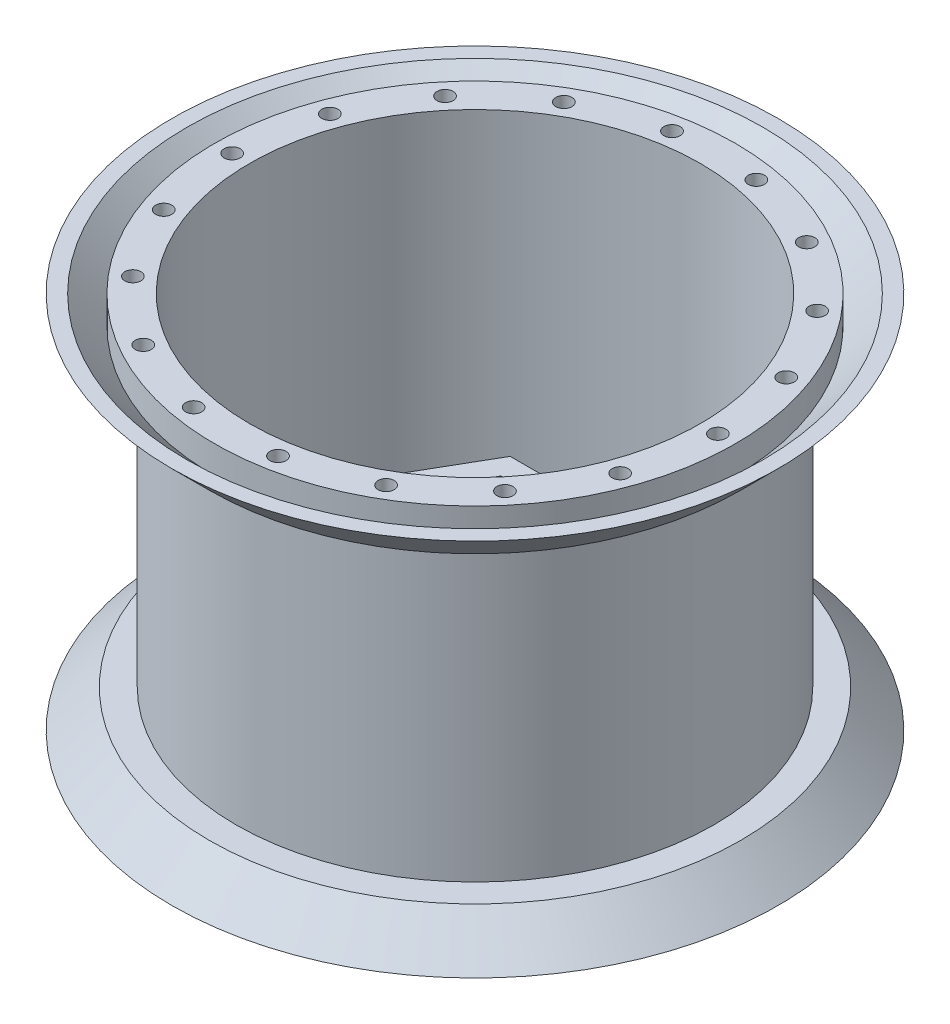
SolidWorks part; units mm, degrees
material "ABS"
ref_plane "Front Plane" through (0, 0, 0) normal (0, 0, 1) x (1, 0, 0)
ref_plane "Top Plane" through (0, 0, 0) normal (0, 1, 0) x (1, 0, 0)
ref_plane "Right Plane" through (0, 0, 0) normal (1, 0, 0) x (0, 0, -1)
sketch "Sketch1" plane through (0, 0, 0) normal (1, 0, 0) x (0, 0, -1)
  line L0 (0, 0) -> (0, 63.5) construction
  line L1 (56.5, 0) -> (54.5, 0)
  line L2 (56.5, 0) -> (49.5, 7)
  line L3 (49.5, 7) -> (44.5, 7)
  line L4 (44.5, 7) -> (44.5, 63.5)
  line L5 (44.5, 35.25) -> (0, 35.25) construction
  line L6 (49.5, 63.5) -> (44.5, 63.5)
  line L7 (56.5, 70.5) -> (49.5, 63.5)
  line L8 (48.5, 5.1716) -> (48.5, 0)
  line L9 (53.6716, 0) -> (48.5, 5.1716)
  line L10 (54.5, 0) -> (53.6716, 0)
  line L11 (55.0858, -1.4142) -> (48.0858, 5.5858) construction
  line L12 (48.5, 0) -> (42, 0)
  line L13 (42, 0) -> (42, 5)
  line L14 (42, 5) -> (19, 21)
  line L15 (19, 21) -> (15, 21)
  line L16 (15, 21) -> (15, 25)
  line L17 (15, 25) -> (9, 25)
  line L18 (0, 0) -> (54.5, 0) construction
  line L19 (48.5, 70.5) -> (42, 70.5)
  line L20 (48.5, 65.3284) -> (48.5, 70.5)
  line L21 (53.6716, 70.5) -> (48.5, 65.3284)
  line L22 (54.5, 70.5) -> (53.6716, 70.5)
  line L23 (56.5, 70.5) -> (54.5, 70.5)
  line L24 (42, 70.5) -> (42, 7.4363)
  line L25 (42, 7.4363) -> (19.6272, 23)
  line L26 (19.6272, 23) -> (17, 23)
  line L27 (17, 23) -> (17, 27)
  line L28 (17, 27) -> (9, 27)
  line L29 (43.1421, 6.6418) -> (19.6272, 23) construction
  line L30 (9, 27) -> (9, 25)
  dimension "D1" = 56.5
  dimension "D2" = 2
  dimension "D3" = 5
  dimension "D4" = 7
  dimension "D5" = 56.5
  dimension "D6" = 0
  dimension "D7" = 8
  dimension "D8" = 0
  dimension "D10" = 6.5
  dimension "D11" = 5
  dimension "D12" = 9
  dimension "D13" = 15
  dimension "D14" = 4
  dimension "D15" = 4
  dimension "D17" = 23
  dimension "D18" = 2
  dimension "D19" = 7
  dimension "D9" = 2
revolve "Revolve1" add sketch "Sketch1" angle 360 about L0
sketch "Sketch2" plane through (0, 27, 0) normal (0, 1, 0) x (1, 0, 0)
  line L0 (8.9489, -15.5) -> (17.8979, 0)
  line L1 (13.2791, 0) -> (6.6395, 11.5)
  line L2 (6.6395, 11.5) -> (-6.6395, 11.5)
  line L3 (-6.6395, 11.5) -> (-13.2791, 0)
  line L4 (-13.2791, 0) -> (-6.6395, -11.5)
  line L5 (-6.6395, -11.5) -> (6.6395, -11.5)
  line L6 (6.6395, -11.5) -> (13.2791, 0)
  line L7 (17.8979, 0) -> (8.9489, 15.5)
  line L8 (8.9489, 15.5) -> (-8.9489, 15.5)
  line L9 (-8.9489, 15.5) -> (-17.8979, 0)
  line L10 (-17.8979, 0) -> (-8.9489, -15.5)
  line L11 (-8.9489, -15.5) -> (8.9489, -15.5)
  circle A0 centre (0, 0) radius 11.5 construction
  dimension "D1" = 23
  dimension "D2" = 4
extrude "Boss-Extrude1" add sketch "Sketch2" along normal blind 5
sketch "Sketch3" plane through (0, 0, 0) normal (0, -1, 0) x (1, 0, 0)
  line L0 (19, 0) -> (42, 0) construction
  circle A0 centre (0, 0) radius 19 construction
  circle A1 centre (0, 0) radius 42 construction
  ellipse E0 centre (30.5, 0) end of major axis (39, 0) minor radius 7.5
  ellipse E1 centre (21.5668, -21.5668) end of major axis (27.5772, -27.5772) minor radius 7.5
  ellipse E2 centre (0, -30.5) end of major axis (0, -39) minor radius 7.5
  ellipse E3 centre (-21.5668, -21.5668) end of major axis (-15.5563, -15.5563) minor radius 7.5
  ellipse E4 centre (-30.5, 0) end of major axis (-39, 0) minor radius 7.5
  ellipse E5 centre (-21.5668, 21.5668) end of major axis (-15.5563, 15.5563) minor radius 7.5
  ellipse E6 centre (0, 30.5) end of major axis (0, 39) minor radius 7.5
  ellipse E7 centre (21.5668, 21.5668) end of major axis (27.5772, 27.5772) minor radius 7.5
  point P58 (0, 0)
  dimension "D1" = 15
  dimension "D2" = 17
extrude "Cut-Extrude1" cut sketch "Sketch3" against normal through all
sketch "Sketch4" plane through (0, 0, 0) normal (0, -1, 0) x (1, 0, 0)
  line L0 (42, 0) -> (48.5, 0) construction
  circle A0 centre (0, 0) radius 42 construction
  circle A1 centre (0, 0) radius 42 construction
  circle A2 centre (0, 0) radius 48.5 construction
  circle A3 centre (45.25, 0) radius 1.5
  circle A4 centre (42.5211, -15.4764) radius 1.5
  circle A5 centre (34.6635, -29.0861) radius 1.5
  circle A6 centre (22.625, -39.1876) radius 1.5
  circle A7 centre (7.8576, -44.5626) radius 1.5
  circle A8 centre (-7.8576, -44.5626) radius 1.5
  circle A9 centre (-22.625, -39.1876) radius 1.5
  circle A10 centre (-34.6635, -29.0861) radius 1.5
  circle A11 centre (-42.5211, -15.4764) radius 1.5
  circle A12 centre (-45.25, 0) radius 1.5
  circle A13 centre (-42.5211, 15.4764) radius 1.5
  circle A14 centre (-34.6635, 29.0861) radius 1.5
  circle A15 centre (-22.625, 39.1876) radius 1.5
  circle A16 centre (-7.8576, 44.5626) radius 1.5
  circle A17 centre (7.8576, 44.5626) radius 1.5
  circle A18 centre (22.625, 39.1876) radius 1.5
  circle A19 centre (34.6635, 29.0861) radius 1.5
  circle A20 centre (42.5211, 15.4764) radius 1.5
  point P48 (0, 0)
  dimension "D1" = 3
  dimension "D2" = 18
extrude "Cut-Extrude2" cut sketch "Sketch4" against normal blind 5
ref_plane "Plane1" through (0, 35.25, 0) normal (0, -1, 0) x (-1, 0, 0)
mirror "Mirror1" about plane through (0, 35.25, 0) normal (0, -1, 0) of "Cut-Extrude2"
